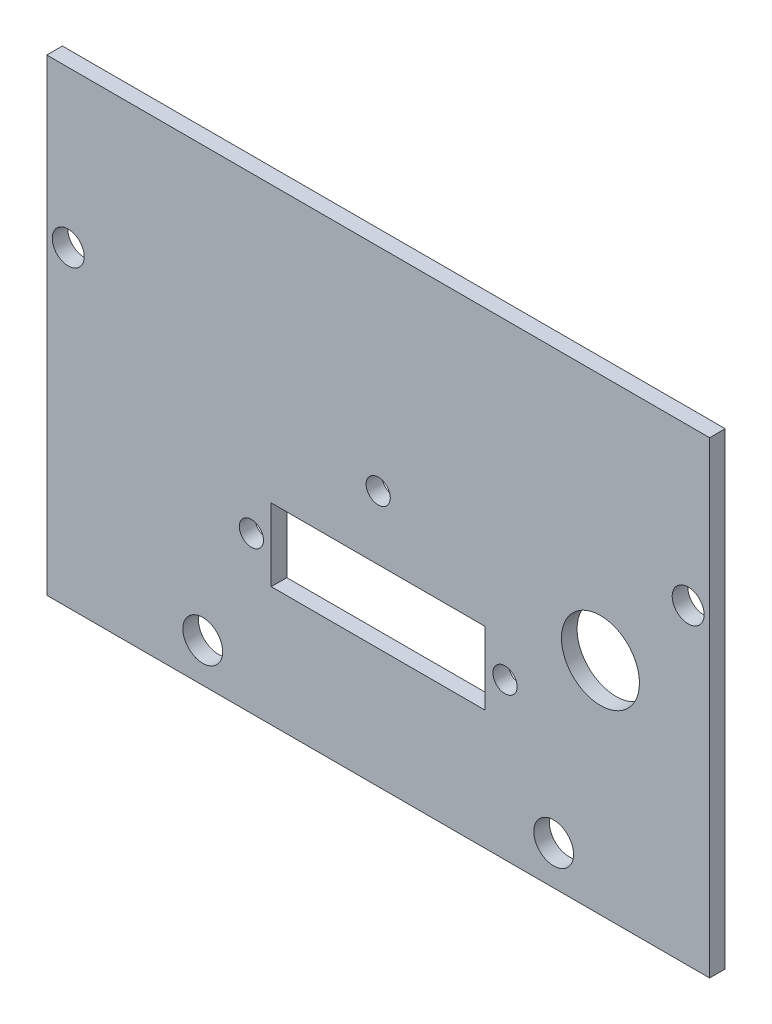
SolidWorks part; units mm, degrees
ref_plane "Front Plane" through (0, 0, 0) normal (0, 0, 1) x (1, 0, 0)
ref_plane "Top Plane" through (0, 0, 0) normal (0, 1, 0) x (1, 0, 0)
ref_plane "Right Plane" through (0, 0, 0) normal (1, 0, 0) x (0, 0, -1)
sketch "Sketch1" plane through (0, 0, 0) normal (0, 0, 1) x (1, 0, 0)
  line L1 (-57.6928, 22.4996) -> (27.3072, 22.4996)
  line L2 (-57.6928, 22.4996) -> (-57.6928, -37.5004)
  line L3 (-57.6928, -37.5004) -> (27.3072, -37.5004)
  line L4 (27.3072, 22.4996) -> (27.3072, -37.5004)
  dimension "D1" = 85
  dimension "D2" = 60
extrude "Boss-Extrude1" add sketch "Sketch1" along normal blind 2
sketch "Sketch2" plane through (0, 0, 0) normal (0, 0, -1) x (-1, 0, 0)
  line L0 (57.6928, -37.5004) -> (-27.3072, -37.5004) construction
  line L1 (-27.3072, -37.5004) -> (-27.3072, 22.4996) construction
  line L2 (57.6928, 22.4996) -> (57.6928, -37.5004) construction
  circle A0 centre (-7.3072, -32.5004) radius 2.55
  circle A1 centre (37.6928, -32.5004) radius 2.55
  dimension "D3" = 5.1
  dimension "D4" = 5.1
  dimension "D5" = 20
  dimension "D6" = 20
  dimension "D1" = 5
  dimension "D2" = 5
extrude "Cut-Extrude1" cut sketch "Sketch2" against normal up to next
sketch "Sketch3" plane through (0, 0, 0) normal (0, 0, -1) x (-1, 0, 0)
  line L0 (-27.3072, 22.4996) -> (57.6928, 22.4996) construction
  line L1 (-22.8072, 10.2496) -> (53.1928, 10.2496) construction
  line L2 (-22.8072, 10.2496) -> (-22.8072, -36.7504) construction
  line L3 (-22.8072, -36.7504) -> (53.1928, -36.7504) construction
  line L4 (53.1928, 10.2496) -> (53.1928, -36.7504) construction
  line L5 (1.4728, -12.8504) -> (28.9128, -12.8504)
  line L6 (1.4728, -12.8504) -> (1.4728, -22.1504)
  line L7 (1.4728, -22.1504) -> (28.9128, -22.1504)
  line L8 (28.9128, -12.8504) -> (28.9128, -22.1504)
  line L9 (57.6928, 22.4996) -> (57.6928, -37.5004) construction
  circle A0 centre (-13.3072, -9.2404) radius 5
  circle A1 centre (15.1928, -4.6704) radius 1.55
  circle A2 centre (-1.0672, -17.5004) radius 1.55
  circle A3 centre (31.4528, -17.5004) radius 1.55
  dimension "D3" = 10
  dimension "D4" = 9.5
  dimension "D5" = 27.51
  dimension "D6" = 3.1
  dimension "D7" = 3.1
  dimension "D8" = 3.1
  dimension "D9" = 38
  dimension "D10" = 32.08
  dimension "D11" = 19.25
  dimension "D13" = 21.74
  dimension "D14" = 54.26
  dimension "D19" = 40
  dimension "D20" = 42.5
  dimension "D1" = 76
  dimension "D2" = 47
  dimension "D12" = 19.25
  dimension "D15" = 14.6
  dimension "D16" = 23.9
  dimension "D17" = 24.28
  dimension "D18" = 51.72
extrude "Cut-Extrude2" cut sketch "Sketch3" against normal up to next
sketch "Sketch4" plane through (0, 0, 2) normal (0, 0, 1) x (1, 0, 0)
  line L0 (27.3072, 22.4996) -> (-57.6928, 22.4996) construction
  line L1 (-57.6928, 22.4996) -> (-57.6928, -37.5004) construction
  line L2 (27.3072, -37.5004) -> (27.3072, 22.4996) construction
  circle A0 centre (-54.9428, 2.4996) radius 2.05
  circle A1 centre (24.5572, 2.4996) radius 2.05
  dimension "D1" = 20
  dimension "D2" = 20
  dimension "D3" = 4.1
  dimension "D4" = 4.1
  dimension "D5" = 2.75
  dimension "D6" = 2.75
extrude "Cut-Extrude3" cut sketch "Sketch4" against normal up to next
